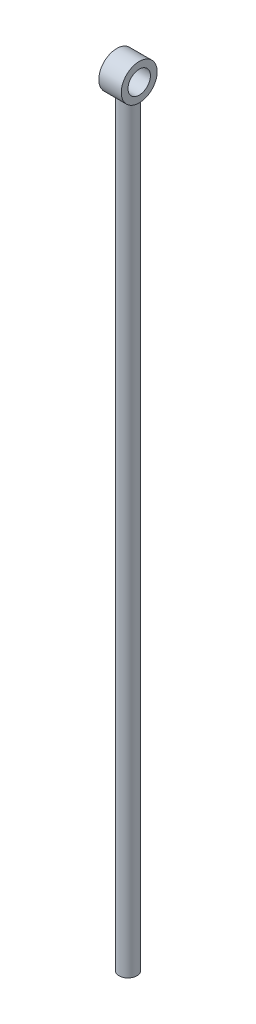
SolidWorks part; units mm, degrees
ref_plane "Front Plane" through (0, 0, 0) normal (0, 0, 1) x (1, 0, 0)
ref_plane "Top Plane" through (0, 0, 0) normal (0, 1, 0) x (1, 0, 0)
ref_plane "Right Plane" through (0, 0, 0) normal (1, 0, 0) x (0, 0, -1)
sketch "Sketch1" plane through (0, 0, 0) normal (1, 0, 0) x (0, 0, -1)
  circle A0 centre (0, 0) radius 3.175
  circle A1 centre (0, 0) radius 5.08
  dimension "D1" = 6.35
  dimension "D2" = 10.16
extrude "Boss-Extrude1" add sketch "Sketch1" along normal mid plane 6.35
ref_plane "Plane1" through (0, -3.302, 0) normal (0, 1, 0) x (1, 0, 0)
sketch "Sketch2" plane through (0, -3.302, 0) normal (0, 1, 0) x (1, 0, 0)
  circle A0 centre (0, 0) radius 2.54
  dimension "D1" = 5.08
extrude "Boss-Extrude2" add sketch "Sketch2" against normal blind 215.9
